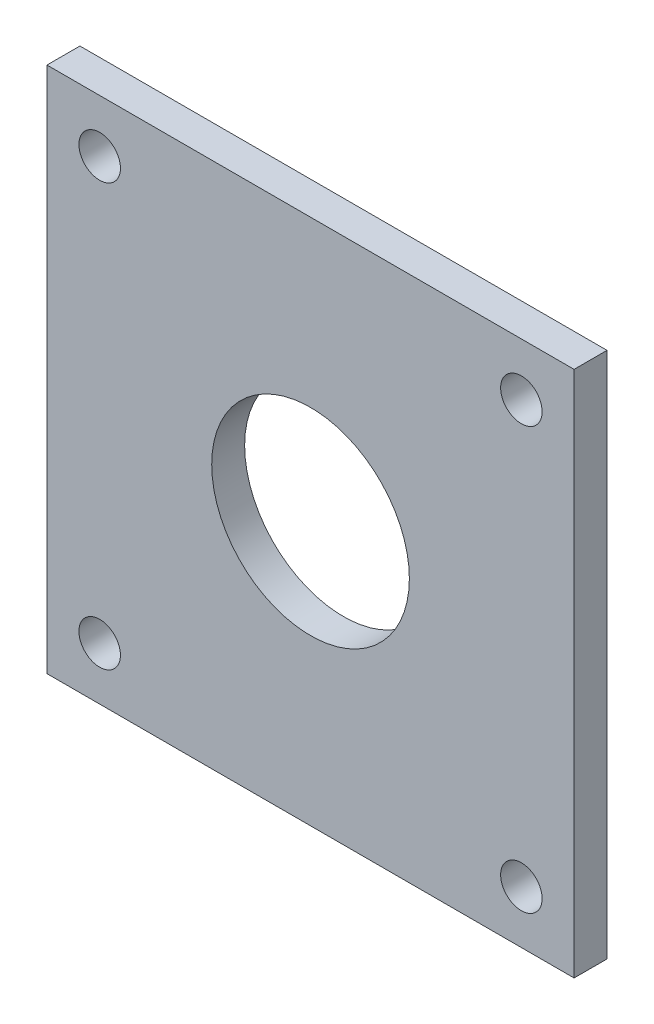
SolidWorks part; units mm, degrees
ref_plane "Front Plane" through (0, 0, 0) normal (0, 0, 1) x (1, 0, 0)
ref_plane "Top Plane" through (0, 0, 0) normal (0, 1, 0) x (1, 0, 0)
ref_plane "Right Plane" through (0, 0, 0) normal (1, 0, 0) x (0, 0, -1)
sketch "Sketch2" plane through (0, 0, 0) normal (0, 0, 1) x (1, 0, 0)
  line L1 (0, 0) -> (50.8, 0)
  line L2 (0, 0) -> (0, 50.8)
  line L3 (0, 50.8) -> (50.8, 50.8)
  line L4 (50.8, 0) -> (50.8, 50.8)
  circle A0 centre (5.08, 45.72) radius 2
  circle A1 centre (45.72, 45.72) radius 2
  circle A2 centre (45.72, 5.08) radius 2
  circle A3 centre (5.08, 5.08) radius 2
  circle A4 centre (25.4, 25.4) radius 9.525
  dimension "D3" = 4
  dimension "D6" = 19.05
  dimension "D1" = 50.8
  dimension "D2" = 50.8
  dimension "D4" = 5.08
  dimension "D5" = 5.08
  dimension "D7" = 5.08
  dimension "D8" = 5.08
extrude "Boss-Extrude1" add sketch "Sketch2" along normal blind 3.175
sketch "Sketch3" plane through (0, 0, 0) normal (0, -1, 0) x (1, 0, 0)
  line L1 (0, 3.175) -> (50.8, 3.175)
  line L2 (0, 3.175) -> (0, 0)
  line L3 (0, 0) -> (50.8, 0)
  line L4 (50.8, 3.175) -> (50.8, 0)
